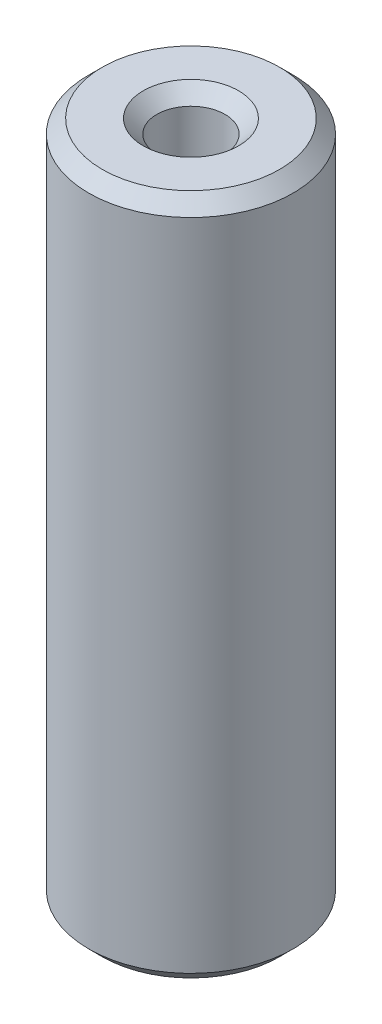
SolidWorks part; units mm, degrees
ref_plane "Plan de face" through (0, 0, 0) normal (0, 0, 1) x (1, 0, 0)
ref_plane "Plan de dessus" through (0, 0, 0) normal (0, 1, 0) x (1, 0, 0)
ref_plane "Plan de droite" through (0, 0, 0) normal (1, 0, 0) x (0, 0, -1)
sketch "Esquisse1" plane through (0, 0, 0) normal (0, 1, 0) x (1, 0, 0)
  circle A0 centre (0, 0) radius 7.5
  circle A1 centre (0, 0) radius 2.5
  dimension "D1" = 15
  dimension "D2" = 5
extrude "Extrusion1" add sketch "Esquisse1" along normal blind 50
chamfer "Chanfrein1" distance 1 angle 45 4 edges at (0, 0, 2.5) (0, 0, 7.5) (0, 50, 2.5) (0, 50, 7.5)
